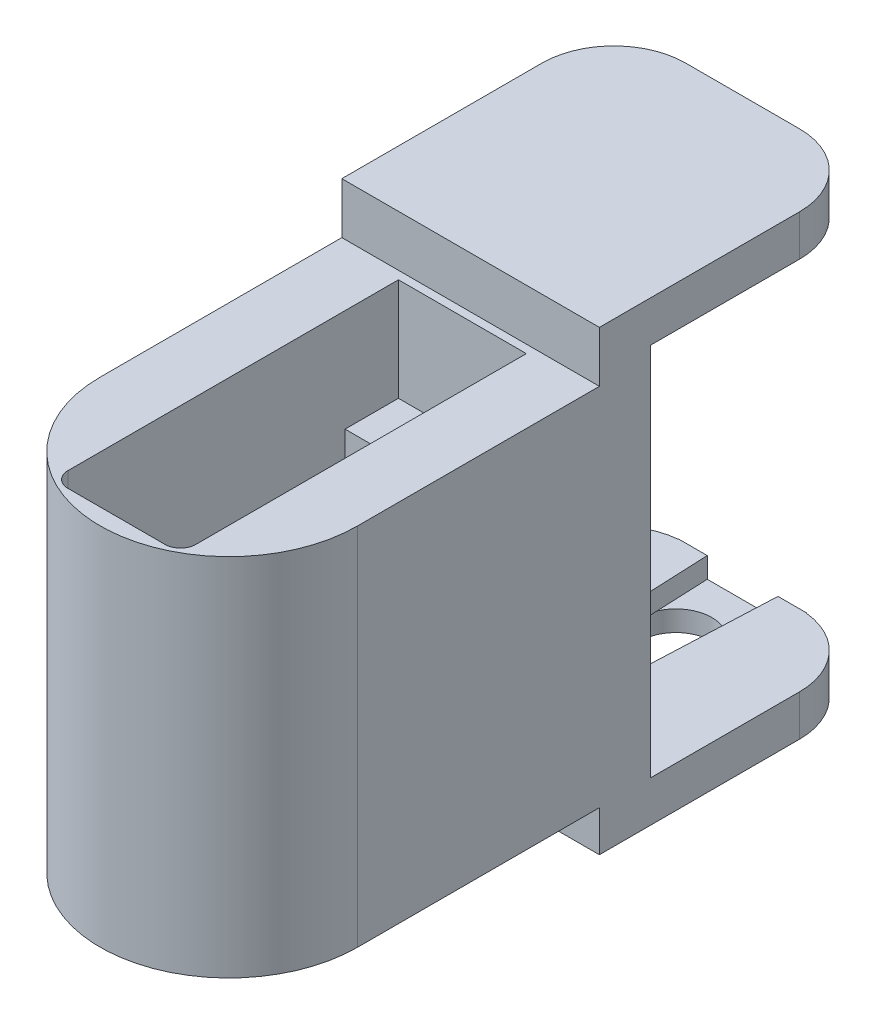
SolidWorks part; units mm, degrees
ref_plane "Front Plane" through (0, 0, 0) normal (0, 0, 1) x (1, 0, 0)
ref_plane "Top Plane" through (0, 0, 0) normal (0, 1, 0) x (1, 0, 0)
ref_plane "Right Plane" through (0, 0, 0) normal (1, 0, 0) x (0, 0, -1)
sketch "Sketch4" plane through (0, 0, 0) normal (0, 0, 1) x (1, 0, 0)
  line L1 (-6.23, -9.975) -> (6.23, -9.975)
  line L2 (-6.23, -9.975) -> (-6.23, 7.275)
  line L3 (-6.23, 7.275) -> (6.23, 7.275)
  line L4 (6.23, -9.975) -> (6.23, 7.275)
  point P4 (0, 7.275)
  dimension "D1" = 12.46
  dimension "D2" = 17.25
  dimension "D3" = 9.975
extrude "Boss-Extrude3" add sketch "Sketch4" along normal blind 6
sketch "Sketch8" plane through (0, -9.975, 0) normal (0, -1, 0) x (-1, 0, 0)
  circle A0 centre (0, -23.55) radius 12.5468
  circle A1 centre (0, -23.55) radius 11.15
  dimension "D1" = 22.3
  dimension "D2" = 23.55
extrude "Boss-Extrude6" add sketch "Sketch8" along normal blind 8.3 and the other way up to surface (17.25 mm away) other way up to face at (0, 7.275, 3)
sketch "Sketch5" plane through (0, 7.275, 0) normal (0, 1, 0) x (1, 0, 0)
  line L8 (12.5468, -23.55) -> (12.5468, 0)
  line L9 (12.5468, 0) -> (6.23, 0)
  line L10 (-12.5468, -23.55) -> (-12.5468, 0)
  line L11 (-12.5468, 0) -> (-6.23, 0)
  line L12 (-6.23, 0) -> (-6.23, -29.7)
  line L14 (6.23, -29.7) -> (6.23, 0)
  line L15 (-6.23, -29.7) -> (6.23, -29.7)
  line L16 (6.23, -6) -> (-6.23, -6) construction
  circle A0 centre (0, -23.55) radius 12.5468 construction
  arc A1 (-12.5468, -23.55) -> (12.5468, -23.55) centre (0, -23.55) ccw
  dimension "D1" = 23.7
  dimension "D2" = 23.55
extrude "Boss-Extrude4" add sketch "Sketch5" against normal up to surface (17.25 mm away) up to face at (0, -9.975, 3)
sketch "Sketch6" plane through (0, 7.275, 0) normal (0, 1, 0) x (1, 0, 0)
  line L0 (6.23, -6) -> (-6.23, -6) construction
  line L3 (6.23, -29.7) -> (-6.23, -29.7) construction
  circle A0 centre (0, -3.6) radius 0.75
  circle A1 centre (0, -32.1) radius 0.75
  dimension "D1" = 1.5
  dimension "D3" = 1.5
  dimension "D2" = 2.4
  dimension "D4" = 2.4
extrude "Cut-Extrude1" cut sketch "Sketch6" against normal blind 5
chamfer "Chamfer1" distance 0.5 angle 60 2 edges at (0, 7.275, 4.35) (0, 7.275, 32.85)
sketch "Sketch10" plane through (0, 7.275, 0) normal (0, 1, 0) x (1, 0, 0)
  line L1 (-6.23, -6) -> (6.23, -6)
  line L2 (-6.23, -6) -> (-6.23, -29.7)
  line L3 (-6.23, -29.7) -> (6.23, -29.7)
  line L4 (6.23, -6) -> (6.23, -29.7)
extrude "Cut-Extrude3" cut sketch "Sketch10" against normal up to surface (17.25 mm away) up to face at (0, -9.975, 10.3399)
ref_plane "Plane1" through (0, 0, 36.0968) normal (0, 0, 1) x (1, 0, 0)
sketch "Sketch13" plane through (0, -18.275, 0) normal (0, -1, 0) x (1, 0, 0)
  line L0 (-12.5468, 23.55) -> (-12.5468, 0)
  line L1 (-12.5468, 0) -> (12.5468, 0)
  line L2 (12.5468, 0) -> (12.5468, 23.55)
  arc A0 (-12.5468, 23.55) -> (12.5468, 23.55) centre (0, 23.55) ccw
  point P3 (0, 0)
extrude "Boss-Extrude7" add sketch "Sketch13" against normal up to surface (8.3 mm away) up to face at (0, -9.975, 10.3399)
sketch "Sketch15" plane through (0, 7.275, 0) normal (0, 1, 0) x (1, 0, 0)
  line L0 (-12.5468, 0) -> (12.5468, 0)
  line L1 (12.5468, 0) -> (12.5468, -23.55)
  line L2 (-12.5468, 0) -> (-12.5468, -23.55)
  line L3 (6.23, -6) -> (6.23, -29.7) construction
  line L4 (-6.23, -0.8) -> (6.23, -0.8)
  line L5 (-6.23, -0.8) -> (-6.23, -33)
  line L6 (-4.73, -34.5) -> (4.73, -34.5)
  line L7 (6.23, -0.8) -> (6.23, -33)
  arc A0 (-12.5468, -23.55) -> (12.5468, -23.55) centre (0, -23.55) ccw
  circle A1 centre (0, -3.6) radius 0.75 construction
  arc A2 (4.73, -34.5) -> (6.23, -33) centre (4.73, -33) ccw
  arc A3 (-6.23, -33) -> (-4.73, -34.5) centre (-4.73, -33) ccw
  point P15 (0, -0.8)
  dimension "D1" = 0.8
  dimension "D3" = 1.5
  dimension "D2" = 2.8
  dimension "D4" = 0
  dimension "D5" = 34.5
extrude "Boss-Extrude9" add sketch "Sketch15" along normal blind 10
sketch "Sketch20" plane through (0, -18.275, 0) normal (0, -1, 0) x (1, 0, 0)
  circle A0 centre (0, 23.55) radius 7.15
  circle A1 centre (0, 23.55) radius 11.15
  circle A2 centre (0, 23.55) radius 11.15 construction
  dimension "D1" = 14.3
extrude "Boss-Extrude11" add sketch "Sketch20" against normal up to surface (8.3 mm away) up to face at (0, -9.975, 27.1007)
sketch "Sketch21" plane through (0, -18.275, 0) normal (0, -1, 0) x (1, 0, 0)
  circle A0 centre (0, 23.55) radius 7.15
  circle A1 centre (0, 23.55) radius 10.15
  circle A2 centre (0, 23.55) radius 7.15 construction
  dimension "D1" = 20.3
extrude "Cut-Extrude7" cut sketch "Sketch21" against normal blind 1.3
sketch "Sketch11" plane through (0, 0, 29.7) normal (0, 0, 1) x (1, 0, 0)
  line L1 (-5, -9.975) -> (5, -9.975)
  line L2 (-5, -9.975) -> (-5, -11.975)
  line L3 (-5, -11.975) -> (5, -11.975)
  line L4 (5, -9.975) -> (5, -11.975)
  line L5 (3.6469, -9.975) -> (6.23, -9.975) construction
  point P4 (0, -9.975)
  dimension "D1" = 0
  dimension "D2" = 10
  dimension "D3" = 2
extrude "Cut-Extrude4" cut sketch "Sketch11" against normal up to surface (23.7 mm away) up to face at (0, -1.35, 6)
sketch "Sketch24" plane through (0, -18.275, 0) normal (0, -1, 0) x (1, 0, 0)
  line L0 (6.23, 20.0415) -> (6.23, 6) construction
  line L1 (-6.23, 6) -> (6.23, 6)
  line L2 (-6.23, 6) -> (-6.23, 12)
  line L3 (-6.23, 12) -> (6.23, 12)
  line L4 (6.23, 6) -> (6.23, 12)
  dimension "D1" = 6
extrude "Cut-Extrude8" cut sketch "Sketch24" against normal up to next
sketch "Sketch17" plane through (-12.5468, 4.7282, 0) normal (1, 0, 0) x (0, -1, 0)
  line L0 (26.9782, 26.5) -> (26.9782, 0)
  line L1 (26.9782, 0) -> (-17.5218, 0)
  line L2 (-17.5218, 0) -> (-17.5218, 26.5)
  line L3 (-17.5218, 26.5) -> (-13.5218, 26.5)
  line L4 (-13.5218, 26.5) -> (-13.5218, 5)
  line L5 (-13.5218, 5) -> (22.9782, 5)
  line L6 (22.9782, 5) -> (22.9782, 26.5)
  line L7 (22.9782, 26.5) -> (26.9782, 26.5)
  point P2 (4.7282, 5)
  point P10 (4.7282, 0)
  dimension "D1" = 4
  dimension "D2" = 36.5
  dimension "D3" = 0
  dimension "D4" = 26.5
  dimension "D5" = 5
extrude "Boss-Extrude10" add sketch "Sketch17" along normal up to surface (25.0936 mm away) up to face at (12.5468, -0.5, 11.775)
sketch "Sketch18" plane through (0, -18.25, 0) normal (0, 1, 0) x (0, 0, 1)
  line L0 (-26.5, -12.5468) -> (-26.5, 12.5468) construction
  line L1 (-26.5, 6.2191) -> (-5, 6.2191)
  line L2 (-26.5, 6.2191) -> (-26.5, -6.2191)
  line L3 (-26.5, -6.2191) -> (-5, -6.2191)
  line L4 (-5, 6.2191) -> (-5, -6.2191)
  line L5 (-5, -12.5468) -> (-5, 12.5468) construction
  point P6 (-26.5, 0)
  point P7 (-26.5, 0)
  dimension "D1" = 0
extrude "Cut-Extrude5" cut sketch "Sketch18" against normal blind 2
sketch "Sketch19" plane through (0, -20.25, 0) normal (0, 1, 0) x (0, 0, 1)
  line L0 (-26.5, -12.5468) -> (-26.5, 12.5468) construction
  line L1 (-26.5, 12.5468) -> (-26.5, -12.5468) construction
  circle A0 centre (-20, 0) radius 3.5
  point P8 (-26.5, 0)
  dimension "D1" = 7
  dimension "D2" = 6.5
extrude "Cut-Extrude6" cut sketch "Sketch19" against normal through all both and the other way through all
fillet "Fillet1" radius 7 4 edges at (12.5468, -20.25, -26.5) (-12.5468, -20.25, -26.5) (12.5468, 20.25, -26.5) (-12.5468, 20.25, -26.5)
ref_plane "Plane2" through (0, 0, 0) normal (1, 0, 0) x (0, 0, -1)
ref_plane "Plane3" through (0, -0.5, 0) normal (0, -1, 0) x (-1, 0, 0)
sketch "Sketch22" plane through (0, 22.25, 0) normal (0, 1, 0) x (1, 0, 0)
  circle A0 centre (0, 20) radius 6.5
  dimension "D1" = 13
extrude "Boss-Extrude12" add sketch "Sketch22" against normal blind 5
sketch "Sketch23" plane through (0, 17.25, 0) normal (0, -1, 0) x (1, 0, 0)
  circle A0 centre (0, -20) radius 6.075
  dimension "D1" = 12.15
extrude "Boss-Extrude13" add sketch "Sketch23" along normal blind 5
fillet "Fillet2" radius 1 1 edges at (0, 12.25, -26.075)
sketch "Sketch25" plane through (0, -20.25, 0) normal (0, 1, 0) x (1, 0, 0)
  line L0 (-6.2191, 5) -> (-2.5, 5)
  line L1 (12.5468, 5) -> (-12.5468, 5) construction
  line L2 (-2.5, 5) -> (-3.1585, 20)
  line L3 (-3.1585, 20) -> (-3.4438, 26.5)
  line L4 (-3.4438, 26.5) -> (-6.2191, 26.5)
  line L5 (-6.2191, 26.4676) -> (-6.2191, 5) construction
  line L6 (-6.2191, 26.5) -> (-6.2191, 5)
  line L7 (6.2191, 5) -> (2.5, 5)
  line L8 (2.5, 5) -> (3.1585, 20)
  line L9 (3.1585, 20) -> (3.4438, 26.5)
  line L10 (3.4438, 26.5) -> (6.2191, 26.5)
  line L11 (6.2191, 5) -> (6.2191, 26.4676) construction
  line L12 (6.2191, 26.5) -> (6.2191, 5)
  line L13 (0, -23.6775) -> (0, 23.6775) construction
  line L14 (5.5468, 26.5) -> (-5.5468, 26.5) construction
  circle A0 centre (0, 20) radius 3.5 construction
  dimension "D1" = 5
  dimension "D2" = 2.5
  dimension "D3" = 3.1585
  dimension "D4" = 6.317
  dimension "D5" = 0
  dimension "D6" = 0
extrude "Boss-Extrude15" add sketch "Sketch25" along normal up to surface (2 mm away) up to face at (9.7194, -18.25, -14.2975)
sketch "Sketch26" plane through (0, -22.25, 0) normal (0, -1, 0) x (-1, 0, 0)
  circle A0 centre (0, 10) radius 0.75
  circle A1 centre (0, 20) radius 3.5 construction
  dimension "D1" = 1.5
  dimension "D2" = 10
  dimension "D3" = 0
extrude "Cut-Extrude9" cut sketch "Sketch26" against normal up to next
